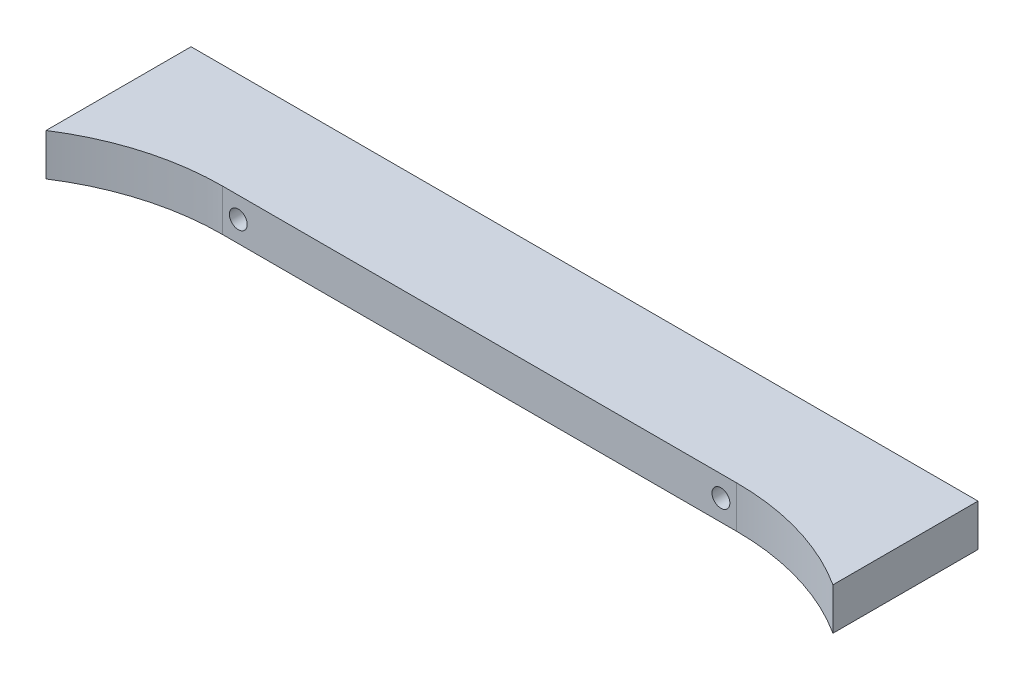
SolidWorks part; units mm, degrees
ref_plane "前视基准面" through (0, 0, 0) normal (0, 0, 1) x (1, 0, 0)
ref_plane "上视基准面" through (0, 0, 0) normal (0, 1, 0) x (1, 0, 0)
ref_plane "右视基准面" through (0, 0, 0) normal (1, 0, 0) x (0, 0, -1)
sketch "草图1" plane through (0, 0, 0) normal (0, 1, 0) x (1, 0, 0)
  line L0 (-49, -10) -> (49, -10)
  line L1 (-75, -10) -> (75, -10)
  line L2 (-75, -10) -> (-75, 10)
  line L3 (-75, 10) -> (75, 10)
  line L4 (75, -10) -> (75, 10)
  line L5 (-75, -10) -> (75, 10) construction
  line L6 (-75, 10) -> (75, -10) construction
  line L7 (-75, -17.6515) -> (-75, -10)
  line L8 (75, -17.6515) -> (75, -10)
  arc A0 (-49, -10) -> (-75, -17.6515) centre (-49, -58) ccw
  arc A1 (49, -10) -> (75, -17.6515) centre (49, -58) cw
  point P0 (0, 0)
  point P9 (0, -10)
  dimension "D4" = 48
  dimension "D5" = 48
  dimension "D1" = 150
  dimension "D2" = 20
  dimension "D3" = 98
extrude "凸台-拉伸1" add sketch "草图1" along normal blind 8 contours L1 L4 L3 L2 L0 | A0 L1 L7 | L1 A1 L8
sketch "草图2" plane through (0, 0, -10) normal (0, 0, -1) x (-1, 0, 0)
  line L0 (-46, 4) -> (46, 4) construction
  line L1 (-75, 8) -> (-75, 0) construction
  circle A0 centre (46, 4) radius 1.5
  circle A1 centre (-46, 4) radius 1.5
  point P3 (0, 4)
  point P6 (-75, 4)
  dimension "D2" = 3
  dimension "D1" = 92
hole_wizard "M3 六角凹头螺钉的柱形沉头孔1" positions "3D草图1" profile "草图3" counterbore size "M3" standard "ISO" end condition through all
sketch3d "3D草图1"
  point P0 (46, 4, -10)
  point P3 (-46, 4, -10)
sketch "草图3" plane through (46, 4, -10) normal (1, 0, 0) x (0, 1, 0)
  line L0 (0, 0) -> (0, 27.6515)
  line L1 (0, 27.6515) -> (1.7, 27.6515)
  line L3 (1.7, 27.6515) -> (1.7, 16)
  line L4 (1.7, 16) -> (3.25, 16)
  line L5 (3.25, 16) -> (3.25, 0)
  line L7 (3.25, 0) -> (0, 0)
  line L11 (0, -6.35) -> (0, 107.95) construction
  dimension "通孔孔直径" = 3.4
  dimension "通孔孔深度" = 27.6515
  dimension "柱形沉头孔直径" = 6.5
  dimension "柱形沉头孔深度" = 16
sketch "草图4" plane through (0, 0, -10) normal (0, 0, -1) x (-1, 0, 0)
  line L0 (-55, 4) -> (55, 4) construction
  circle A0 centre (-55, 4) radius 2.6
  circle A1 centre (55, 4) radius 2.6
  point P3 (0, 4)
  dimension "D2" = 5.2
  dimension "D1" = 110
extrude "切除-拉伸1" cut sketch "草图4" against normal blind 10
